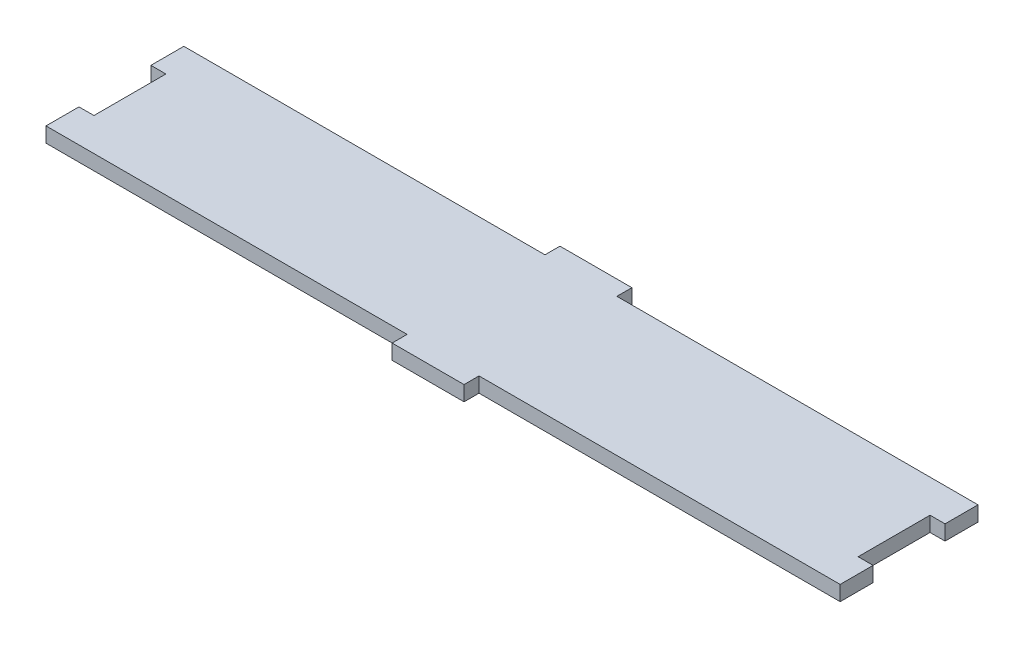
SolidWorks part; units mm, degrees
ref_plane "Front Plane" through (0, 0, 0) normal (0, 0, 1) x (1, 0, 0)
ref_plane "Top Plane" through (0, 0, 0) normal (0, 1, 0) x (1, 0, 0)
ref_plane "Right Plane" through (0, 0, 0) normal (1, 0, 0) x (0, 0, -1)
sketch "Sketch1" plane through (0, 0, 0) normal (0, 1, 0) x (1, 0, 0)
  line L0 (-183.515, 0) -> (-336.55, 0)
  line L1 (0, 0) -> (-153.035, 0)
  line L2 (0, 0) -> (0, -58.42)
  line L3 (0, -58.42) -> (-153.035, -58.42)
  line L4 (-336.55, 0) -> (-336.55, -58.42)
  line L6 (-153.035, -58.42) -> (-153.035, -64.77)
  line L7 (-153.035, -64.77) -> (-183.515, -64.77)
  line L8 (-183.515, -58.42) -> (-183.515, -64.77)
  line L10 (-183.515, 0) -> (-183.515, 6.35)
  line L11 (-183.515, 6.35) -> (-153.035, 6.35)
  line L12 (-153.035, 0) -> (-153.035, 6.35)
  line L13 (-183.515, -58.42) -> (-336.55, -58.42)
  point P17 (-166.4609, 0)
  point P18 (-167.7366, 0)
  point P19 (-166.9483, 0)
  dimension "D1" = 336.55
  dimension "D2" = 58.42
  dimension "D4" = 30.48
  dimension "D5" = 6.35
  dimension "D7" = 30.48
  dimension "D8" = 6.35
extrude "Boss-Extrude1" add sketch "Sketch1" along normal blind 6.35 contours L0 L4 L13 L8 L7 L6 L3 L2 L1 L12 L11 L10
sketch "Sketch2" plane through (0, 6.35, 0) normal (0, 1, 0) x (1, 0, 0)
  line L0 (-336.55, 0) -> (-336.55, -58.42) construction
  line L1 (-336.55, -13.97) -> (-330.2, -13.97)
  line L2 (-336.55, -13.97) -> (-336.55, -44.45)
  line L3 (-336.55, -44.45) -> (-330.2, -44.45)
  line L4 (-330.2, -13.97) -> (-330.2, -44.45)
  line L5 (0, 0) -> (0, -58.42) construction
  line L6 (0, -13.97) -> (-6.35, -13.97)
  line L7 (0, -13.97) -> (0, -44.45)
  line L8 (0, -44.45) -> (-6.35, -44.45)
  line L9 (-6.35, -13.97) -> (-6.35, -44.45)
  point P12 (0, -29.21)
  point P13 (0, -29.21)
  point P14 (-336.55, -29.21)
  point P15 (-336.55, -29.21)
  dimension "D1" = 6.35
  dimension "D2" = 30.48
  dimension "D3" = 0
  dimension "D4" = 30.48
  dimension "D5" = 6.35
  dimension "D6" = 0
extrude "Cut-Extrude1" cut sketch "Sketch2" against normal through all
